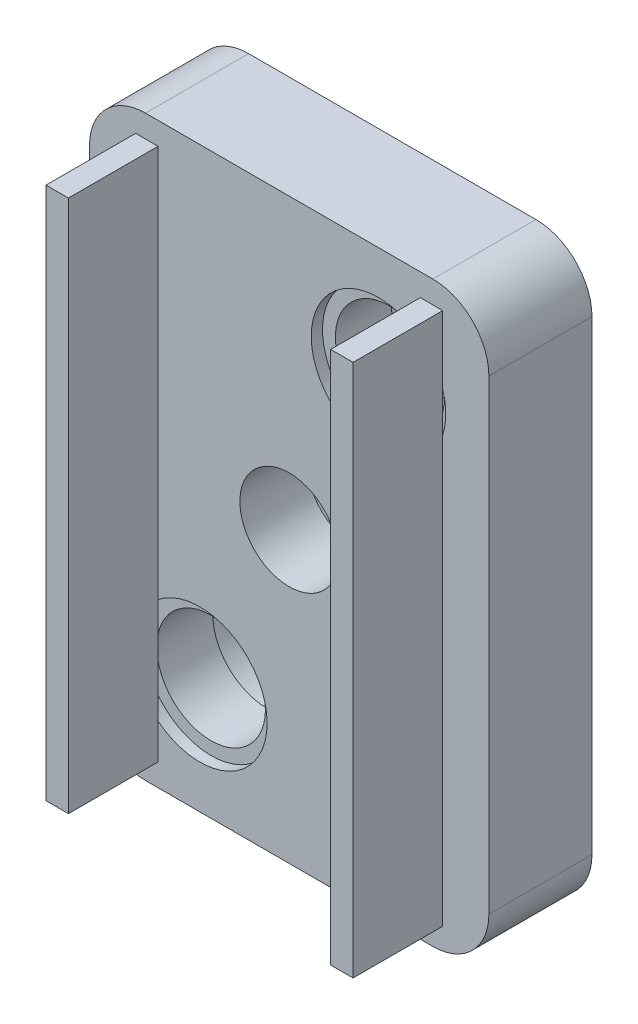
SolidWorks part; units mm, degrees
ref_plane "Front Plane" through (0, 0, 0) normal (0, 0, 1) x (1, 0, 0)
ref_plane "Top Plane" through (0, 0, 0) normal (0, 1, 0) x (1, 0, 0)
ref_plane "Right Plane" through (0, 0, 0) normal (1, 0, 0) x (0, 0, -1)
sketch "Sketch1" plane through (0, 0, 0) normal (0, 0, 1) x (1, 0, 0)
  line L1 (2.5, 0) -> (15.32, 0)
  line L2 (0, 2.5) -> (0, 23.29)
  line L3 (2.5, 25.79) -> (15.32, 25.79)
  line L4 (17.82, 2.5) -> (17.82, 23.29)
  circle A0 centre (4.925, 20.865) radius 2.425 construction
  circle A1 centre (4.925, 12.895) radius 2.425 construction
  circle A2 centre (4.925, 4.925) radius 2.425 construction
  circle A3 centre (12.895, 4.925) radius 2.425 construction
  arc A4 (0, 23.29) -> (2.5, 25.79) centre (2.5, 23.29) cw
  arc A5 (2.5, 0) -> (0, 2.5) centre (2.5, 2.5) cw
  arc A6 (15.32, 0) -> (17.82, 2.5) centre (15.32, 2.5) ccw
  arc A7 (15.32, 25.79) -> (17.82, 23.29) centre (15.32, 23.29) cw
  point P11 (0, 0)
  point P18 (0, 0)
  dimension "D1" = 4.85
  dimension "D2" = 2.5
  dimension "D3" = 2.5
  dimension "D4" = 7.97
  dimension "D5" = 7.97
  dimension "D6" = 2.5
  dimension "D7" = 7.97
  dimension "D8" = 2.5
  dimension "D9" = 2.5
  dimension "D10" = 2.5
  dimension "D11" = 2.5
  dimension "D12" = 2.5
extrude "Boss-Extrude1" add sketch "Sketch1" along normal blind 4.6
sketch "Sketch4" plane through (0, 0, 4.6) normal (0, 0, 1) x (1, 0, 0)
  line L1 (0, 23.29) -> (0, 2.5) construction
  line L3 (2.5, 0) -> (15.32, 0) construction
  line L5 (15.32, 25.79) -> (2.5, 25.79) construction
  circle A1 centre (4.925, 4.925) radius 2.425
  circle A3 centre (12.895, 20.865) radius 2.425
  point P8 (0, 0)
  point P9 (0, 0)
  point P13 (0, 0)
  dimension "D1" = 4.85
  dimension "D2" = 7.97
  dimension "D3" = 2.5
  dimension "D4" = 2.5
  dimension "D5" = 2.5
extrude "Cut-Extrude1" cut sketch "Sketch4" against normal blind 14.6
sketch "Sketch5" plane through (0, 0, 0) normal (0, 0, -1) x (-1, 0, 0)
  circle A0 centre (-12.895, 20.865) radius 3
  circle A2 centre (-4.925, 4.925) radius 3
  dimension "D1" = 6
extrude "Cut-Extrude2" cut sketch "Sketch5" against normal blind 1.6
sketch "Sketch6" plane through (0, 0, 4.6) normal (0, 0, 1) x (1, 0, 0)
  circle A0 centre (4.925, 4.925) radius 3
  circle A1 centre (12.895, 20.865) radius 3
  dimension "D1" = 6
extrude "Cut-Extrude3" cut sketch "Sketch6" against normal blind 0.5
sketch "Sketch7" plane through (0, 0, 4.6) normal (0, 0, 1) x (1, 0, 0)
  line L0 (17.82, 2.5) -> (17.82, 23.29) construction
  line L1 (2.5, 0) -> (15.32, 0) construction
  circle A0 centre (8.91, 12.895) radius 2.2
  point P4 (17.82, 12.895)
  point P7 (8.91, 0)
  dimension "D1" = 4.4
extrude "Cut-Extrude4" cut sketch "Sketch7" against normal blind 3
sketch "Sketch8" plane through (0, 0, 4.6) normal (0, 0, 1) x (1, 0, 0)
  line L0 (0, 23.29) -> (0, 2.5) construction
  line L1 (2.06, 24.79) -> (3.06, 24.79)
  line L2 (2.06, 24.79) -> (2.06, 1)
  line L3 (2.06, 1) -> (3.06, 1)
  line L4 (3.06, 24.79) -> (3.06, 1)
  line L5 (15.76, 1) -> (14.76, 1)
  line L6 (15.76, 1) -> (15.76, 24.79)
  line L7 (15.76, 24.79) -> (14.76, 24.79)
  line L8 (14.76, 1) -> (14.76, 24.79)
  line L10 (2.5, 0) -> (15.32, 0) construction
  line L11 (15.32, 25.79) -> (2.5, 25.79) construction
  dimension "D1" = 11.7
  dimension "D2" = 1
  dimension "D3" = 1
  dimension "D4" = 2.06
  dimension "D5" = 1
  dimension "D6" = 1
extrude "Boss-Extrude2" add sketch "Sketch8" along normal blind 4
